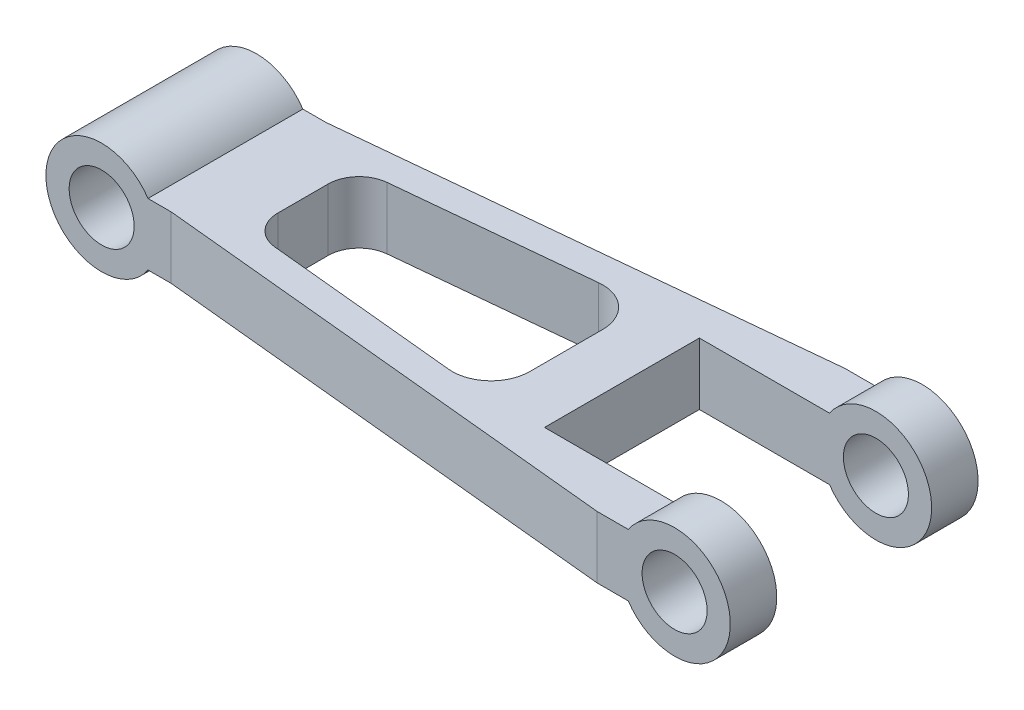
SolidWorks part; units mm, degrees
ref_plane "Front Plane" through (0, 0, 0) normal (0, 0, 1) x (1, 0, 0)
ref_plane "Top Plane" through (0, 0, 0) normal (0, 1, 0) x (1, 0, 0)
ref_plane "Right Plane" through (0, 0, 0) normal (1, 0, 0) x (0, 0, -1)
sketch "Sketch1" plane through (0, 0, 0) normal (0, 0, 1) x (1, 0, 0)
  line L0 (0, 0) -> (400, 0) construction
  line L1 (29.9333, 20) -> (370.0667, 20)
  line L2 (29.9333, -20) -> (370.0667, -20)
  line L4 (0, 20) -> (400, 20) construction
  line L5 (0, -20) -> (400, -20) construction
  arc A0 (29.9333, 20) -> (29.9333, -20) centre (0, 0) ccw
  circle A3 centre (0, 0) radius 21
  arc A5 (370.0667, -20) -> (370.0667, 20) centre (400, 0) ccw
  circle A6 centre (400, 0) radius 21
  dimension "D1" = 72
  dimension "D3" = 42
  dimension "D6" = 42
  dimension "D7" = 72
  dimension "D2" = 400
  dimension "D4" = 20
  dimension "D5" = 20
extrude "Boss-Extrude1" add sketch "Sketch1" along normal blind 160
sketch "Sketch3" plane through (0, 20, 0) normal (0, 1, 0) x (1, 0, 0)
  line L0 (-36, -30) -> (-36, 0)
  line L1 (0, 0) -> (0, -160) construction
  line L2 (436, -160) -> (436, 0)
  line L3 (400, -160) -> (400, 0)
  line L4 (-36, -80) -> (538.3987, -80) construction
  line L5 (-36, -30) -> (538.3987, -30) construction
  line L6 (-36, -130) -> (538.3987, -130) construction
  line L8 (350, 0) -> (-36, 0)
  line L9 (44.9333, -30) -> (-36, -30)
  line L10 (0, -30) -> (0, -160) construction
  line L11 (350, -160) -> (350, 0)
  line L12 (350, -160) -> (44.9333, -130)
  line L13 (29.9333, -30) -> (29.9333, 0) construction
  line L14 (350, 0) -> (44.9333, -30)
  line L20 (44.9333, -130) -> (-36, -130)
  line L21 (-36, -130) -> (-36, -160)
  line L22 (-36, -160) -> (350, -160)
  line M6 (370.0667, 0) -> (29.9333, 0)
  line M7 (29.9333, 0) -> (29.9333, -160)
  line M8 (29.9333, -160) -> (370.0667, -160)
  dimension "D5" = 30
  dimension "D1" = 50
  dimension "D6" = 15
  dimension "D7" = 15
  dimension "D2" = 36
  dimension "D3" = 50
  dimension "D4" = 50
extrude "Cut-Extrude3" cut sketch "Sketch3" against normal through all both and the other way through all contours L14 L9 M6 M7 | L9 L8 L0 M7 | L21 L22 L20 M7 | L12 L20 M7 M8
sketch "Sketch5" plane through (0, 20, 0) normal (0, 1, 0) x (1, 0, 0)
  line L0 (-36, -30) -> (-36, -130)
  line L2 (-36, -56.469) -> (348.8426, -56.469) construction
  line L3 (250, -56.469) -> (250, -103.531)
  line L4 (222.5533, -31.589) -> (98.0427, -43.8333)
  line L5 (222.5533, -128.411) -> (98.0427, -116.1667)
  line L6 (44.9333, -30) -> (350, 0) construction
  line L7 (44.9333, -130) -> (350, -160) construction
  line L9 (80, -30) -> (80, -130) construction
  line L11 (-36, -103.531) -> (348.8426, -103.531) construction
  line L12 (0, -30) -> (0, -130)
  line L13 (80, -63.7373) -> (80, -96.2627)
  line L14 (250, -30) -> (250, -130) construction
  arc A0 (250, -56.469) -> (222.5533, -31.589) centre (225, -56.469) ccw
  arc A1 (222.5533, -128.411) -> (250, -103.531) centre (225, -103.531) ccw
  arc A2 (80, -63.7373) -> (98.0427, -43.8333) centre (100, -63.7373) cw
  arc A3 (80, -96.2627) -> (98.0427, -116.1667) centre (100, -96.2627) ccw
  point P4 (-36, -80)
  point P5 (348.8426, -80)
  dimension "D6" = 50
  dimension "D7" = 50
  dimension "D8" = 20
  dimension "D9" = 20
  dimension "D3" = 36
  dimension "D4" = 80
  dimension "D5" = 250
extrude "Cut-Extrude4" cut sketch "Sketch5" against normal through all both and the other way through all contours L13 A3 L5 A1 L3 A0 L4 A2
sketch "Sketch6" plane through (0, 20, 0) normal (0, 1, 0) x (1, 0, 0)
  line L0 (436, 0) -> (436, -160)
  line L1 (436, -80) -> (552.8151, -80) construction
  line L3 (286, -130) -> (586, -130)
  line L4 (286, -130) -> (286, -30)
  line L5 (286, -30) -> (586, -30)
  line L6 (586, -130) -> (586, -30)
  line L7 (286, -130) -> (586, -30) construction
  line L8 (286, -30) -> (586, -130) construction
  line M18 (370.0667, -160) -> (370.0667, 0)
  dimension "D1" = 100
  dimension "D2" = 300
extrude "Cut-Extrude5" cut sketch "Sketch6" against normal through all both and the other way through all contours L5 L4 L3 M18
